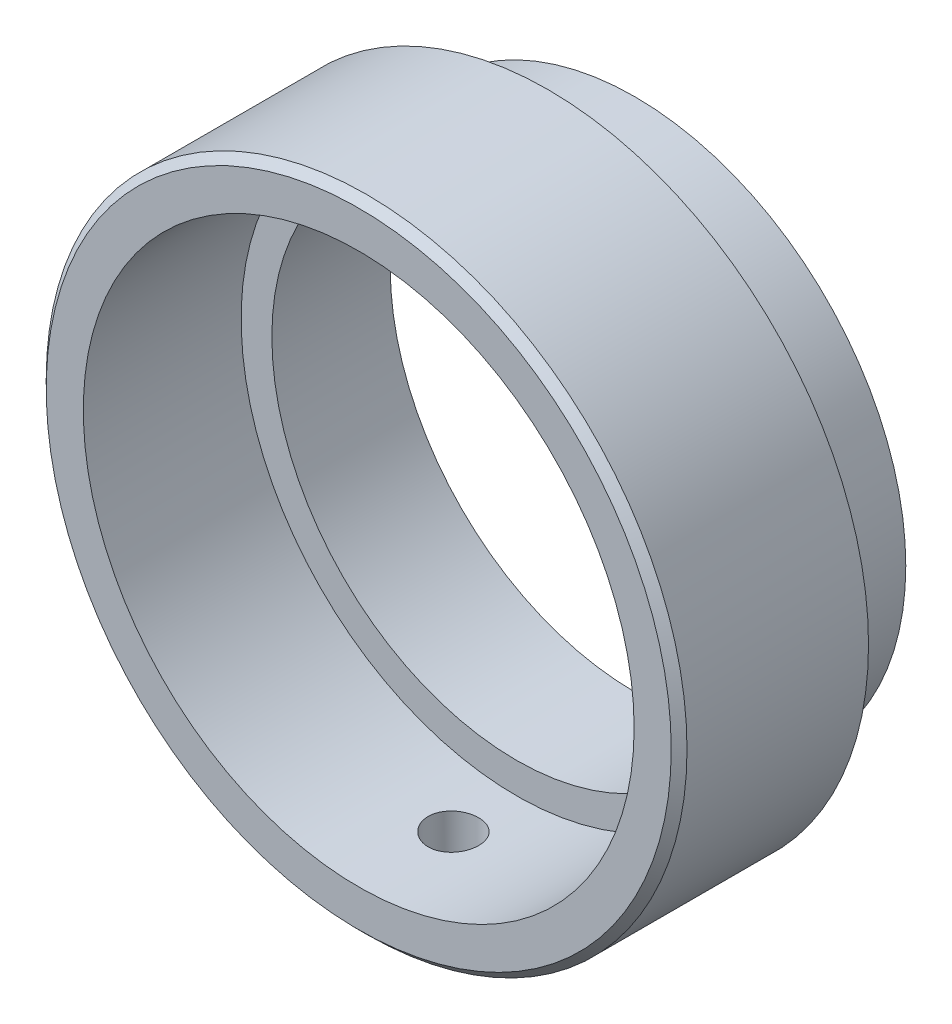
SolidWorks part; units mm, degrees
ref_plane "Front Plane" through (0, 0, 0) normal (0, 0, 1) x (1, 0, 0)
ref_plane "Top Plane" through (0, 0, 0) normal (0, 1, 0) x (1, 0, 0)
ref_plane "Right Plane" through (0, 0, 0) normal (1, 0, 0) x (0, 0, -1)
sketch "Sketch1" plane through (0, 0, 0) normal (0, 1, 0) x (1, 0, 0)
  line L0 (-17.45, 0) -> (-19.8, 0)
  line L1 (-20.3, 0.5) -> (-20.3, 12)
  line L2 (-20.3, 12) -> (-17.1608, 12)
  line L3 (-17.1608, 12) -> (-17.1608, 13.5)
  line L4 (-17.1608, 13.5) -> (-16.7608, 13.5)
  line L5 (-16.7608, 13.5) -> (-16.7608, 14)
  line L6 (-16.7608, 14) -> (-17.1608, 14)
  line L7 (-17.1608, 14) -> (-17.1608, 17.5)
  line L8 (-17.1608, 17.5) -> (-15.5039, 17.5)
  line L10 (-19.8, 0) -> (-20.3, 0.5)
  line L11 (-17.45, 0) -> (-17.45, 10)
  line L12 (-17.45, 10) -> (-15.5039, 10)
  line L13 (-15.5039, 10) -> (-15.5039, 17.5)
  line L14 (0, 0) -> (0, 26.2514) construction
  point P1 (-20.3, 0)
  point P3 (-16.9608, 13.5)
  dimension "D1" = 17.45
  dimension "D2" = 13.5
  dimension "D3" = 4
  dimension "D4" = 0.5
  dimension "D5" = 0.4
  dimension "D6" = 1.5
  dimension "D7" = 10
  dimension "D9" = 20.3
  dimension "D10" = 15.5039
  dimension "D11" = 17.1608
  dimension "D12" = 16.7608
  dimension "D13" = 17.45
revolve "Revolve1" add sketch "Sketch1" angle 360 about L14
ref_plane "Plane1" through (0, 0, 0) normal (0, 1, 0) x (1, 0, 0)
sketch "Sketch2" plane through (0, 0, 0) normal (0, 1, 0) x (1, 0, 0)
  line L0 (17.1608, 13.5) -> (-17.1608, 13.5) construction
  circle A0 centre (0, 6) radius 1.6
  dimension "D1" = 3.2
  dimension "D2" = 6
  dimension "D3" = 7.5
extrude "Cut-Extrude1" cut sketch "Sketch2" against normal blind 25
cosmetic thread "Cosmetic Thread1" parameters "D2"=4
